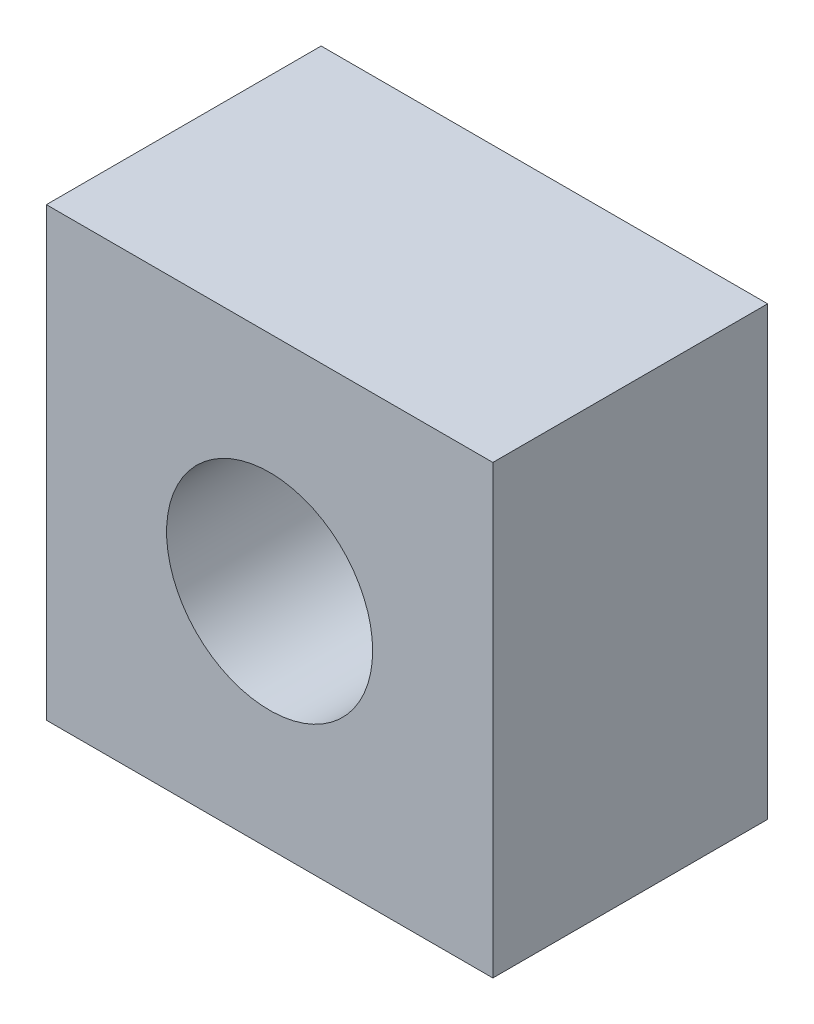
SolidWorks part; units mm, degrees
ref_plane "Front Plane" through (0, 0, 0) normal (0, 0, 1) x (1, 0, 0)
ref_plane "Top Plane" through (0, 0, 0) normal (0, 1, 0) x (1, 0, 0)
ref_plane "Right Plane" through (0, 0, 0) normal (1, 0, 0) x (0, 0, -1)
sketch "Sketch1" plane through (0, 0, 0) normal (0, 0, 1) x (1, 0, 0)
  line L1 (0, 0) -> (13, 0)
  line L2 (0, 0) -> (0, 13)
  line L3 (0, 13) -> (13, 13)
  line L4 (13, 0) -> (13, 13)
  dimension "D1" = 13
  dimension "D2" = 13
extrude "Boss-Extrude1" add sketch "Sketch1" along normal blind 8 contours L3 L4 L1 L2
sketch "Sketch2" plane through (0, 0, 8) normal (0, 0, 1) x (1, 0, 0)
  line L0 (13, 0) -> (13, 13) construction
  line L3 (13, 14) -> (0, 14) construction
  circle A0 centre (6.5, 6.5) radius 3
  point P6 (2.2472, 14)
  dimension "D3" = 6
  dimension "D1" = 6.5
  dimension "D2" = 7.5
extrude "Cut-Extrude1" cut sketch "Sketch2" against normal blind 8 contours A0
